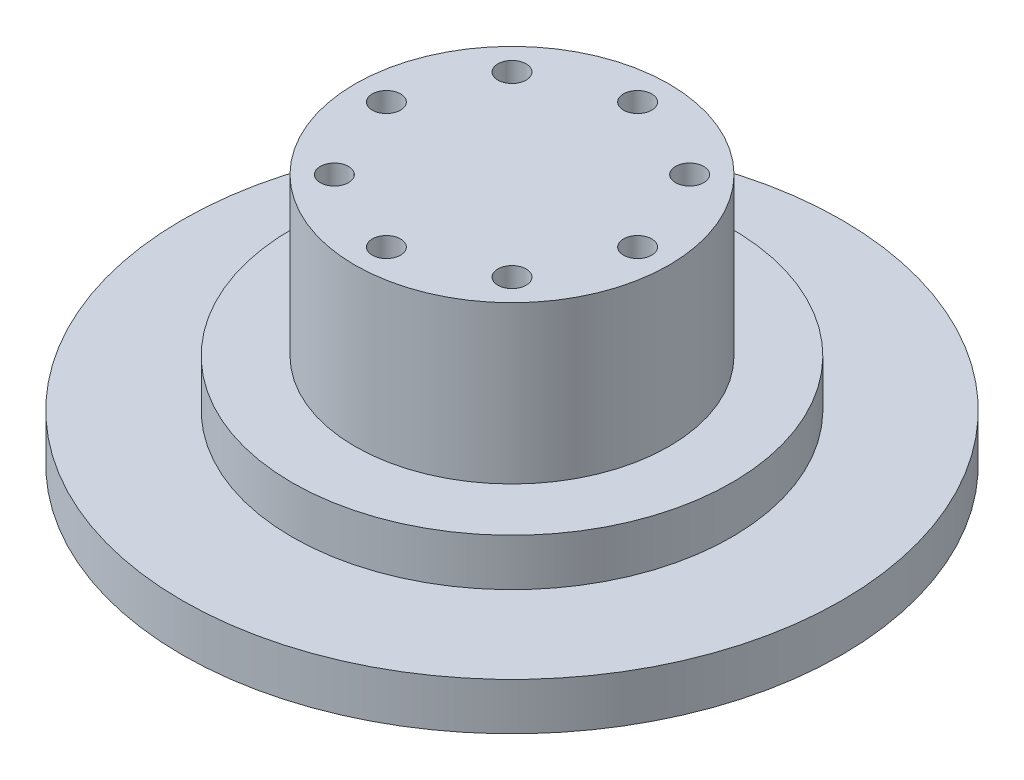
SolidWorks part; units mm, degrees
ref_plane "정면" through (0, 0, 0) normal (0, 0, 1) x (1, 0, 0)
ref_plane "윗면" through (0, 0, 0) normal (0, 1, 0) x (1, 0, 0)
ref_plane "우측면" through (0, 0, 0) normal (1, 0, 0) x (0, 0, -1)
sketch "스케치1" plane through (0, 0, 0) normal (0, 1, 0) x (1, 0, 0)
  circle A0 centre (0, 0) radius 21
  dimension "D1" = 42
extrude "보스-돌출1" add sketch "스케치1" along normal blind 3
sketch "스케치2" plane through (0, 3, 0) normal (0, 1, 0) x (1, 0, 0)
  circle A0 centre (0, 0) radius 10
  dimension "D1" = 20
extrude "보스-돌출2" add sketch "스케치2" along normal blind 13
sketch "스케치3" plane through (0, 3, 0) normal (0, 1, 0) x (1, 0, 0)
  circle A0 centre (0, 0) radius 14
extrude "보스-돌출3" add sketch "스케치3" along normal blind 3
sketch "스케치4" plane through (0, 0, 0) normal (0, -1, 0) x (1, 0, 0)
  line L0 (0, 0) -> (8, 0) construction
  line L1 (8, 0) -> (0, -8) construction
  line L2 (0, -8) -> (-8, 0) construction
  line L3 (-8, 0) -> (0, 8) construction
  line L4 (0, 8) -> (8, 0) construction
  line L5 (8, 0) -> (0, 0) construction
  line L6 (0, 0) -> (5.6569, 5.6569) construction
  line L7 (5.6569, 5.6569) -> (-5.6569, -5.6569) construction
  line L8 (-5.6569, -5.6569) -> (0, 0) construction
  line L9 (0, 0) -> (5.6569, -5.6569) construction
  line L10 (5.6569, -5.6569) -> (-5.6569, 5.6569) construction
  circle A0 centre (0, 0) radius 8 construction
  circle A1 centre (8, 0) radius 0.9
  circle A2 centre (5.6569, -5.6569) radius 0.9
  circle A3 centre (5.6569, 5.6569) radius 0.9
  circle A4 centre (0, 8) radius 0.9
  circle A5 centre (-5.6569, 5.6569) radius 0.9
  circle A6 centre (0, -8) radius 0.9
  circle A7 centre (-5.6569, -5.6569) radius 0.9
  circle A8 centre (-8, 0) radius 0.9
  dimension "D1" = 16
  dimension "D2" = 1.8
  dimension "D3" = 1.8
  dimension "D4" = 1.8
extrude "컷-돌출1" cut sketch "스케치4" against normal up to surface (16 mm away) up to face at (0, 16, 10)
